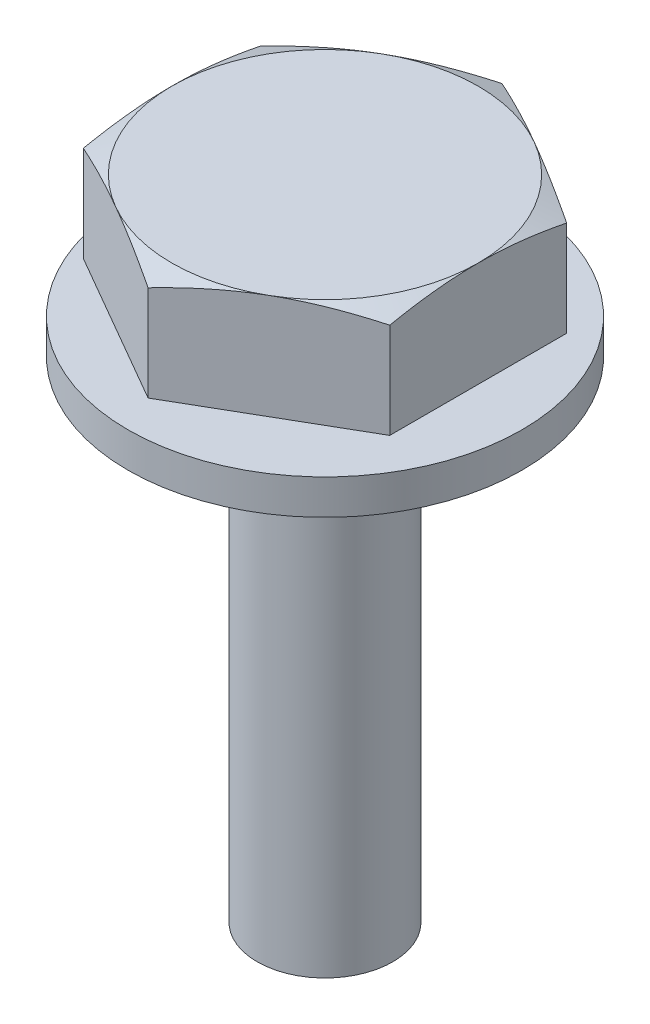
SolidWorks part; units mm, degrees
material "V2A"
ref_plane "Vorne" through (0, 0, 0) normal (0, 0, 1) x (1, 0, 0)
ref_plane "Oben" through (0, 0, 0) normal (0, 1, 0) x (1, 0, 0)
ref_plane "Rechts" through (0, 0, 0) normal (1, 0, 0) x (0, 0, -1)
ref_plane "Scheibe - Dicke" through (0, 0.8, 0) normal (0, 1, 0) x (1, 0, 0)
sketch "Skizze1" plane through (0, 0.8, 0) normal (0, 1, 0) x (1, 0, 0)
  line L0 (0, -4.95) -> (0, 4.95) construction
  line L1 (3.5, 2.0207) -> (0, 4.0415)
  line L2 (0, 4.0415) -> (-3.5, 2.0207)
  line L3 (-3.5, 2.0207) -> (-3.5, -2.0207)
  line L4 (-3.5, -2.0207) -> (0, -4.0415)
  line L5 (0, -4.0415) -> (3.5, -2.0207)
  line L6 (3.5, -2.0207) -> (3.5, 2.0207)
  circle A0 centre (0, 0) radius 3.5 construction
  dimension "SW" = 7
extrude "Kopf" add sketch "Skizze1" along normal blind 2.8
sketch "Skizze3" plane through (0, 0, 0) normal (1, 0, 0) x (0, 0, -1)
  line L0 (4.0415, 3.6) -> (3.5, 3.6)
  line L1 (2.0207, 3.6) -> (4.0415, 3.6) construction
  line L2 (3.5, 3.6) -> (4.0415, 3.3812)
  line L3 (4.0415, 3.6) -> (4.0415, 0.8) construction
  line L4 (4.0415, 3.3812) -> (4.0415, 3.6)
  line L5 (0, 0) -> (0, 3.6) construction
  line L6 (4.0415, 0.8) -> (2.95, 0.8)
  line L7 (4.0415, 0.8) -> (4.0415, 1.2)
  line L8 (4.0415, 1.2) -> (2.95, 1.2)
  line L9 (2.95, 0.8) -> (2.95, 1.2)
  line L10 (-2.0207, 3.6) -> (2.0207, 3.6) construction
  point P18 (2.95, 1)
  dimension "D1" = 7
  dimension "D2" = 5.9
  dimension "D3" = 0.4
  dimension "D4" = 22
revolve "Schnitt Kopf" cut sketch "Skizze3" angle 360 about L5
sketch "Skizze2" plane through (0, 0, 0) normal (0, 0, 1) x (1, 0, 0)
  line L0 (0, 5.0869) -> (0, -30.3726) construction
  line L1 (0, 0.8) -> (1.55, 0.8)
  line L3 (1.55, 0.8) -> (1.55, -11.2)
  line L4 (1.55, -11.2) -> (0, -11.2)
  line L5 (0, 0.8) -> (0, -11.2)
  line L6 (-3.5, 0.8) -> (0, 0.8) construction
  dimension "Länge" = 12
  dimension "D - Kerndurchmesser" = 3.1
revolve "Gewinde" add sketch "Skizze2" angle 360 about L0
cosmetic thread "Gewindedarstellung1" parameters "D2"=3.05
sketch "Skizze4" plane through (0, 0, 0) normal (1, 0, 0) x (0, 0, -1)
  line L0 (-2.95, 0.8) -> (2.95, 0.8) construction
  line L1 (2.15, 0.8) -> (4.5, 0.8)
  line L2 (2.15, 0.8) -> (2.15, 0)
  line L3 (2.15, 0) -> (4.5, 0)
  line L4 (4.5, 0.8) -> (4.5, 0)
  line L5 (0, 0) -> (0, 1.2) construction
  line L6 (-2.0207, 1.2) -> (2.0207, 1.2) construction
  dimension "D1" = 4.3
  dimension "D2" = 9
revolve "Rotation1" add sketch "Skizze4" angle 360 about L5
